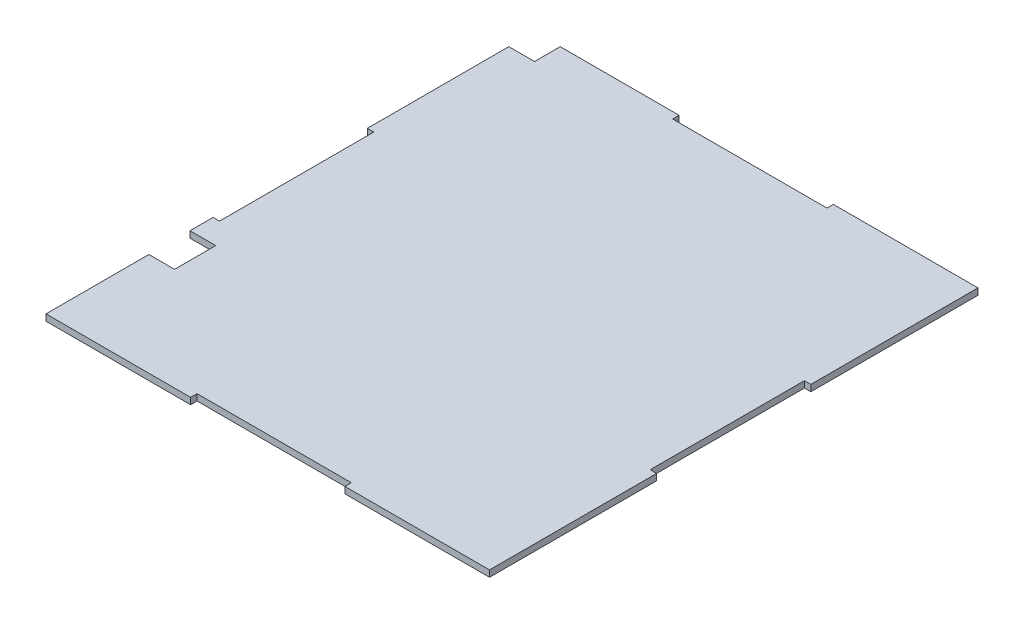
SolidWorks part; units mm, degrees
ref_plane "Front Plane" through (0, 0, 0) normal (0, 0, 1) x (1, 0, 0)
ref_plane "Top Plane" through (0, 0, 0) normal (0, 1, 0) x (1, 0, 0)
ref_plane "Right Plane" through (0, 0, 0) normal (1, 0, 0) x (0, 0, -1)
sketch "Sketch2" plane through (0, 0, 0) normal (0, 1, 0) x (1, 0, 0)
  line L1 (0, 0) -> (219.075, 0)
  line L2 (0, 0) -> (0, 241.3)
  line L3 (0, 241.3) -> (219.075, 241.3)
  line L4 (219.075, 0) -> (219.075, 241.3)
  dimension "D2" = 241.3
  dimension "D1" = 219.075
extrude "Boss-Extrude1" add sketch "Sketch2" along normal blind 3.175
sketch "Sketch3" plane through (0, 3.175, 0) normal (0, 1, 0) x (1, 0, 0)
  line L0 (0, 120.65) -> (1.5875, 120.65) construction
  line L1 (3.175, 158.75) -> (0, 158.75)
  line L2 (3.175, 158.75) -> (3.175, 82.55)
  line L3 (3.175, 82.55) -> (0, 82.55)
  line L4 (0, 158.75) -> (0, 82.55)
  line L5 (3.175, 158.75) -> (0, 82.55) construction
  line L6 (3.175, 82.55) -> (0, 158.75) construction
  line L7 (0, 241.3) -> (0, 0) construction
  line L8 (109.5375, 241.3) -> (109.5375, 120.65) construction
  line L9 (219.075, 241.3) -> (0, 241.3) construction
  line L10 (109.5375, 120.65) -> (219.075, 120.65) construction
  line L11 (219.075, 0) -> (219.075, 241.3) construction
  line L12 (215.9, 82.55) -> (219.075, 158.75) construction
  line L13 (215.9, 158.75) -> (219.075, 82.55) construction
  line L14 (219.075, 120.65) -> (217.4875, 120.65) construction
  line L15 (219.075, 158.75) -> (219.075, 82.55)
  line L16 (215.9, 82.55) -> (219.075, 82.55)
  line L17 (215.9, 158.75) -> (215.9, 82.55)
  line L18 (215.9, 158.75) -> (219.075, 158.75)
  line L19 (71.4375, 3.175) -> (147.6375, 0) construction
  line L20 (71.4375, 241.3) -> (147.6375, 241.3)
  line L21 (71.4375, 241.3) -> (71.4375, 238.125)
  line L22 (71.4375, 238.125) -> (147.6375, 238.125)
  line L23 (147.6375, 241.3) -> (147.6375, 238.125)
  line L24 (71.4375, 241.3) -> (147.6375, 238.125) construction
  line L25 (71.4375, 238.125) -> (147.6375, 241.3) construction
  line L26 (71.4375, 0) -> (147.6375, 3.175) construction
  line L27 (147.6375, 0) -> (147.6375, 3.175)
  line L28 (71.4375, 3.175) -> (147.6375, 3.175)
  line L29 (71.4375, 0) -> (71.4375, 3.175)
  line L30 (71.4375, 0) -> (147.6375, 0)
  point P0 (1.5875, 120.65)
  point P21 (109.5375, 239.7125)
  point P30 (109.5375, 1.5875)
  dimension "D1" = 76.2
  dimension "D2" = 3.175
extrude "Cut-Extrude1" cut sketch "Sketch3" against normal through all
sketch "Sketch4" plane through (0, 3.175, 0) normal (0, 1, 0) x (1, 0, 0)
  line L0 (0, 0) -> (71.4375, 0) construction
  line L1 (0, 71.12) -> (12.7, 71.12)
  line L2 (0, 71.12) -> (0, 50.8)
  line L3 (0, 50.8) -> (12.7, 50.8)
  line L4 (12.7, 71.12) -> (12.7, 50.8)
  line L6 (0, 82.55) -> (0, 0) construction
  line L8 (0, 241.3) -> (12.7, 241.3)
  line L9 (0, 241.3) -> (0, 228.6)
  line L10 (0, 228.6) -> (12.7, 228.6)
  line L11 (12.7, 241.3) -> (12.7, 228.6)
  dimension "D1" = 50.8
  dimension "D2" = 12.7
  dimension "D3" = 20.32
  dimension "D4" = 12.7
  dimension "D5" = 12.7
extrude "Cut-Extrude2" cut sketch "Sketch4" against normal through all
equation "\"depth\"= 7.3"
equation "\"height\"= 9.5"
equation "\"width\"= 8.50"
equation "\"flipWidth\"= 6.5"
equation "\"flipHeight\"= 4"
equation "\"spindleLength\"= 7.75"
equation "\"bearingID\"= 0.1559"
equation "\"bearingOD\"= 0.3539\t"
equation "\"motorWidth\"= 0.79"
equation "\"motorHeight\"= 1.0"
equation "\"motorLength\"= 1.58"
equation "\"spindleMaxDiam\"= 2.75"
equation "\"totalLength\"= 15"
equation "\"D2@Sketch2\"=\"height\""
equation "\"D1@Sketch2\"=\"width\"+1/8"
